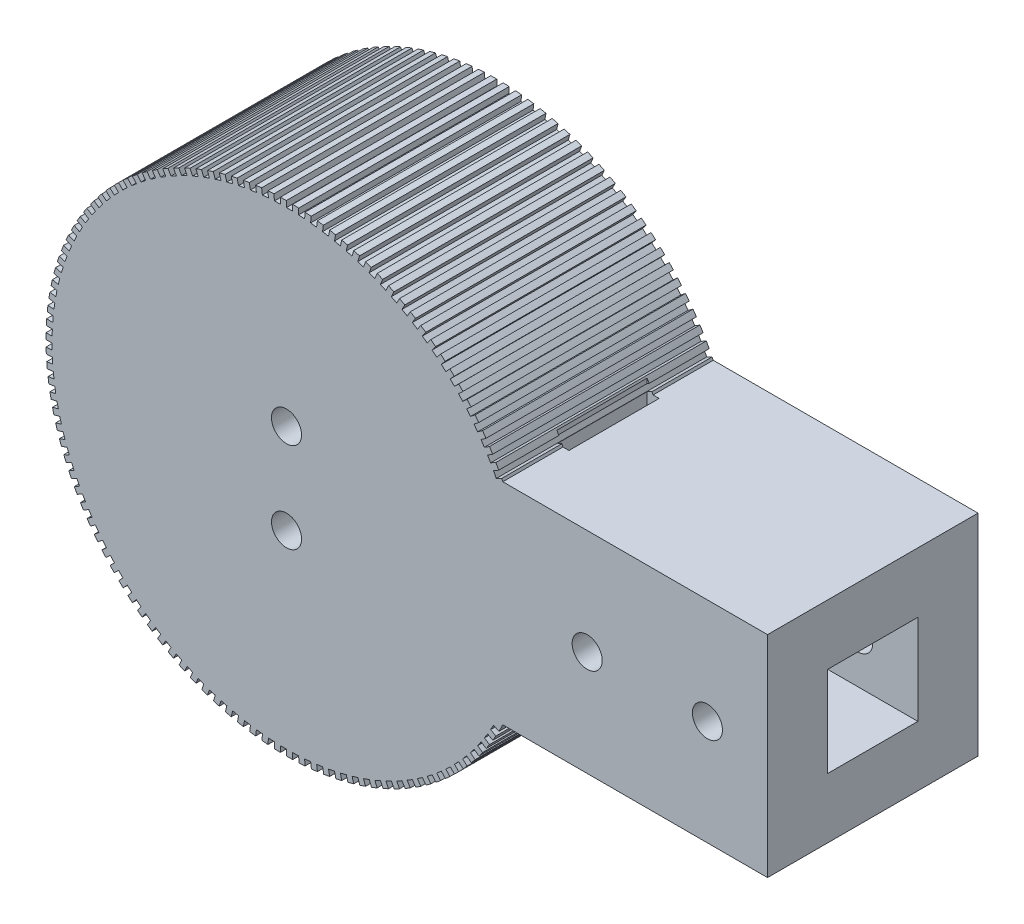
SolidWorks part; units mm, degrees
ref_plane "Front Plane" through (0, 0, 0) normal (0, 0, 1) x (1, 0, 0)
ref_plane "Top Plane" through (0, 0, 0) normal (0, 1, 0) x (1, 0, 0)
ref_plane "Right Plane" through (0, 0, 0) normal (1, 0, 0) x (0, 0, -1)
sketch "Sketch1" plane through (0, 0, 0) normal (0, 0, 1) x (1, 0, 0)
  circle A0 centre (0, 0) radius 40
  dimension "D1" = 80
extrude "Boss-Extrude1" add sketch "Sketch1" along normal blind 35
sketch "Sketch2" plane through (0, 0, 0) normal (1, 0, 0) x (0, 0, -1)
  line L0 (0, 0) -> (-35, 0) construction
  line L1 (-35, 40) -> (-35, -40) construction
  line L2 (0, -40) -> (0, 40) construction
  line L3 (-35, -17.5) -> (0, -17.5)
  line L4 (-35, -17.5) -> (-35, 17.5)
  line L5 (-35, 17.5) -> (0, 17.5)
  line L6 (0, -17.5) -> (0, 17.5)
  line L7 (-35, -17.5) -> (0, 17.5) construction
  line L8 (-35, 17.5) -> (0, -17.5) construction
  line L14 (-27.2632, -9.7632) -> (-6.2129, 11.2871) construction
  line L15 (-25, 12.8571) -> (-10, -12.8571) construction
  point P5 (-17.5, 0)
  point P12 (-17.5, 0)
  dimension "D1" = 35
extrude "Boss-Extrude2" add sketch "Sketch2" along normal blind 80
sketch "Sketch3" plane through (0, 0, 0) normal (0, 0, -1) x (-1, 0, 0)
  circle A0 centre (0, 0) radius 7.5 construction
  circle A1 centre (0, 7.5) radius 2.5
  circle A2 centre (0, -7.5) radius 2.5
  circle A3 centre (0, 0) radius 1.25
  dimension "D1" = 5
  dimension "D2" = 15
extrude "Cut-Extrude1" cut sketch "Sketch3" against normal through all both and the other way through all contours A2 | A1
sketch "Sketch4" plane through (0, 17.5, 0) normal (0, 1, 0) x (1, 0, 0)
  line L0 (35.9687, 0) -> (35.9687, -35) construction
  line L2 (34.9687, -25) -> (36.9687, -25)
  line L3 (34.9687, -25) -> (34.9687, -10)
  line L4 (34.9687, -10) -> (36.9687, -10)
  line L5 (36.9687, -25) -> (36.9687, -10)
  line L6 (34.9687, -25) -> (36.9687, -10) construction
  line L7 (34.9687, -10) -> (36.9687, -25) construction
  point P4 (35.9687, -17.5)
  dimension "D1" = 2
  dimension "D2" = 15
extrude "Cut-Extrude2" cut sketch "Sketch4" against normal through all both and the other way through all
sketch "Sketch6" plane through (80, 0, 0) normal (1, 0, 0) x (0, 0, -1)
  line L0 (-35, 17.5) -> (0, -17.5) construction
  line L2 (-10, -7.5) -> (-25, -7.5)
  line L3 (-10, -7.5) -> (-10, 7.5)
  line L4 (-10, 7.5) -> (-25, 7.5)
  line L5 (-25, -7.5) -> (-25, 7.5)
  line L6 (-10, -7.5) -> (-25, 7.5) construction
  line L7 (-10, 7.5) -> (-25, -7.5) construction
  point P4 (-17.5, 0)
  dimension "D1" = 15
  dimension "D2" = 15
extrude "Cut-Extrude4" cut sketch "Sketch6" against normal blind 47.5
sketch "Sketch7" plane through (0, 0, 35) normal (0, 0, 1) x (1, 0, 0)
  line L1 (80, -17.5) -> (80, 17.5) construction
  line L2 (40, 0) -> (60, 0) construction
  line L3 (60, 0) -> (80, 0) construction
  circle A0 centre (50, 0) radius 2.5
  circle A1 centre (70, 0) radius 2.5
  dimension "D2" = 5
  dimension "D3" = 5
  dimension "D1" = 40
extrude "Cut-Extrude5" cut sketch "Sketch7" against normal through all both and the other way through all
sketch "Sketch8" plane through (0, 0, 35) normal (0, 0, 1) x (1, 0, 0)
  line L0 (0, 0) -> (-40.0066, 0) construction
  line L1 (-39, 0) -> (-40.0066, 0)
  line L2 (-40.0066, 0) -> (-39.9941, 1)
  line L3 (-39.9941, 1) -> (-38.9872, 1)
  line L4 (-38.9483, 2.0077) -> (-39.9536, 2.0595)
  line L5 (-39.9536, 2.0595) -> (-39.8896, 3.0575)
  line L6 (-39.8896, 3.0575) -> (-38.884, 3.0057)
  line L7 (-38.7933, 4.01) -> (-39.7946, 4.1135)
  line L8 (-39.7946, 4.1135) -> (-39.6793, 5.1069)
  line L9 (-39.6793, 5.1069) -> (-38.6777, 5.0034)
  line L10 (-38.5354, 6.0017) -> (-39.5301, 6.1566)
  line L11 (-39.5301, 6.1566) -> (-39.3638, 7.1428)
  line L12 (-39.3638, 7.1428) -> (-38.3689, 6.9878)
  line L13 (-38.1754, 7.9775) -> (-39.1607, 8.1834)
  line L14 (-39.1607, 8.1834) -> (-38.9439, 9.1597)
  line L15 (-38.9439, 9.1597) -> (-37.9583, 8.9538)
  line L16 (-37.7141, 9.9322) -> (-38.6875, 10.1885)
  line L17 (-38.6875, 10.1885) -> (-38.4208, 11.1524)
  line L18 (-38.4208, 11.1524) -> (-37.447, 10.8959)
  line L19 (-37.1528, 11.8605) -> (-38.1117, 12.1666)
  line L20 (-38.1117, 12.1666) -> (-37.7957, 13.1154)
  line L21 (-37.7957, 13.1154) -> (-36.8364, 12.8092)
  line L22 (-36.493, 13.7573) -> (-37.4349, 14.1124)
  line L23 (-37.4349, 14.1124) -> (-37.0704, 15.0437)
  line L24 (-37.0704, 15.0437) -> (-36.1282, 14.6885)
  line L25 (-35.7364, 15.6177) -> (-36.6588, 16.0208)
  line L26 (-36.6588, 16.0208) -> (-36.2469, 16.9321)
  line L27 (-36.2469, 16.9321) -> (-35.3242, 16.5289)
  line L28 (-34.885, 17.4367) -> (-35.7854, 17.8867)
  line L29 (-35.7854, 17.8867) -> (-35.3271, 18.7756)
  line L30 (-35.3271, 18.7756) -> (-34.4264, 18.3254)
  line L31 (-33.9411, 19.2094) -> (-34.8172, 19.7052)
  line L32 (-34.8172, 19.7052) -> (-34.3138, 20.5693)
  line L33 (-34.3138, 20.5693) -> (-33.4374, 20.0733)
  line L34 (-32.9072, 20.9312) -> (-33.7566, 21.4714)
  line L35 (-33.7566, 21.4714) -> (-33.2094, 22.3085)
  line L36 (-33.2094, 22.3085) -> (-32.3597, 21.768)
  line L37 (-31.7861, 22.5974) -> (-32.6065, 23.1807)
  line L38 (-32.6065, 23.1807) -> (-32.0169, 23.9885)
  line L39 (-32.0169, 23.9885) -> (-31.1962, 23.405)
  line L40 (-30.5807, 24.2038) -> (-31.37, 24.8285)
  line L41 (-31.37, 24.8285) -> (-30.7396, 25.6049)
  line L42 (-30.7396, 25.6049) -> (-29.95, 24.9799)
  line L43 (-29.2941, 25.7459) -> (-30.0503, 26.4105)
  line L44 (-30.0503, 26.4105) -> (-29.3807, 27.1533)
  line L45 (-29.3807, 27.1533) -> (-28.6244, 26.4886)
  line L46 (-27.9299, 27.2198) -> (-28.6508, 27.9224)
  line L47 (-28.6508, 27.9224) -> (-27.9439, 28.6298)
  line L48 (-27.9439, 28.6298) -> (-27.2228, 27.927)
  line L49 (-26.4917, 28.6215) -> (-27.1754, 29.3603)
  line L50 (-27.1754, 29.3603) -> (-26.4331, 30.0304)
  line L51 (-26.4331, 30.0304) -> (-25.7491, 29.2914)
  line L52 (-24.9831, 29.9473) -> (-25.628, 30.7203)
  line L53 (-25.628, 30.7203) -> (-24.8521, 31.3513)
  line L54 (-24.8521, 31.3513) -> (-24.207, 30.5781)
  line L55 (-23.4084, 31.1937) -> (-24.0126, 31.9989)
  line L56 (-24.0126, 31.9989) -> (-23.2052, 32.5891)
  line L57 (-23.2052, 32.5891) -> (-22.6008, 31.7837)
  line L58 (-21.7715, 32.3574) -> (-22.3335, 33.1926)
  line L59 (-22.3335, 33.1926) -> (-21.4968, 33.7405)
  line L60 (-21.4968, 33.7405) -> (-20.9347, 32.905)
  line L61 (-20.0769, 33.4353) -> (-20.5951, 34.2983)
  line L62 (-20.5951, 34.2983) -> (-19.7314, 34.8024)
  line L63 (-19.7314, 34.8024) -> (-19.213, 33.9391)
  line L64 (-18.3291, 34.4245) -> (-18.8022, 35.313)
  line L65 (-18.8022, 35.313) -> (-17.9136, 35.772)
  line L66 (-17.9136, 35.772) -> (-17.4404, 34.8831)
  line L67 (-16.5327, 35.3224) -> (-16.9594, 36.2341)
  line L68 (-16.9594, 36.2341) -> (-16.0484, 36.6467)
  line L69 (-16.0484, 36.6467) -> (-15.6215, 35.7347)
  line L70 (-14.6924, 36.1266) -> (-15.0716, 37.0591)
  line L71 (-15.0716, 37.0591) -> (-14.1406, 37.4243)
  line L72 (-14.1406, 37.4243) -> (-13.7612, 36.4915)
  line L73 (-12.8132, 36.8351) -> (-13.1439, 37.7858)
  line L74 (-13.1439, 37.7858) -> (-12.1953, 38.1026)
  line L75 (-12.1953, 38.1026) -> (-11.8645, 37.1515)
  line L76 (-10.8999, 37.4458) -> (-11.1813, 38.4124)
  line L77 (-11.1813, 38.4124) -> (-10.2176, 38.6799)
  line L78 (-10.2176, 38.6799) -> (-9.9362, 37.713)
  line L79 (-8.9578, 37.9573) -> (-9.189, 38.937)
  line L80 (-9.189, 38.937) -> (-8.2129, 39.1546)
  line L81 (-8.2129, 39.1546) -> (-7.9816, 38.1745)
  line L82 (-6.9919, 38.3681) -> (-7.1724, 39.3584)
  line L83 (-7.1724, 39.3584) -> (-6.1864, 39.5254)
  line L84 (-6.1864, 39.5254) -> (-6.0059, 38.5348)
  line L85 (-5.0075, 38.6772) -> (-5.1368, 39.6755)
  line L86 (-5.1368, 39.6755) -> (-4.1435, 39.7915)
  line L87 (-4.1435, 39.7915) -> (-4.0142, 38.7929)
  line L88 (-3.0098, 38.8837) -> (-3.0875, 39.8873)
  line L89 (-3.0875, 39.8873) -> (-2.0895, 39.952)
  line L90 (-2.0895, 39.952) -> (-2.0118, 38.9481)
  line L91 (-1.0042, 38.9871) -> (-1.0301, 39.9934)
  line L92 (-1.0301, 39.9934) -> (-0.0301, 40.0066)
  line L93 (-0.0301, 40.0066) -> (-0.0042, 39)
  line L94 (1.0042, 38.9871) -> (1.0301, 39.9934)
  line L95 (1.0301, 39.9934) -> (2.0294, 39.9551)
  line L96 (2.0294, 39.9551) -> (2.0035, 38.9485)
  line L97 (3.0098, 38.8837) -> (3.0875, 39.8873)
  line L98 (3.0875, 39.8873) -> (4.0836, 39.7977)
  line L99 (4.0836, 39.7977) -> (4.0059, 38.7937)
  line L100 (5.0075, 38.6772) -> (5.1368, 39.6755)
  line L101 (5.1368, 39.6755) -> (6.1269, 39.5347)
  line L102 (6.1269, 39.5347) -> (5.9976, 38.5361)
  line L103 (6.9919, 38.3681) -> (7.1724, 39.3584)
  line L104 (7.1724, 39.3584) -> (8.154, 39.1669)
  line L105 (8.154, 39.1669) -> (7.9734, 38.1762)
  line L106 (8.9578, 37.9573) -> (9.189, 38.937)
  line L107 (9.189, 38.937) -> (10.1594, 38.6952)
  line L108 (10.1594, 38.6952) -> (9.9281, 37.7151)
  line L109 (10.8999, 37.4458) -> (11.1813, 38.4124)
  line L110 (11.1813, 38.4124) -> (12.1379, 38.1209)
  line L111 (12.1379, 38.1209) -> (11.8565, 37.154)
  line L112 (12.8132, 36.8351) -> (13.1439, 37.7858)
  line L113 (13.1439, 37.7858) -> (14.0843, 37.4455)
  line L114 (14.0843, 37.4455) -> (13.7534, 36.4944)
  line L115 (14.6924, 36.1266) -> (15.0716, 37.0591)
  line L116 (15.0716, 37.0591) -> (15.9932, 36.6708)
  line L117 (15.9932, 36.6708) -> (15.6139, 35.738)
  line L118 (16.5327, 35.3224) -> (16.9594, 36.2341)
  line L119 (16.9594, 36.2341) -> (17.8598, 35.7989)
  line L120 (17.8598, 35.7989) -> (17.4329, 34.8869)
  line L121 (18.3291, 34.4245) -> (18.8022, 35.313)
  line L122 (18.8022, 35.313) -> (19.679, 34.832)
  line L123 (19.679, 34.832) -> (19.2057, 33.9432)
  line L124 (20.0769, 33.4353) -> (20.5951, 34.2983)
  line L125 (20.5951, 34.2983) -> (21.446, 33.7728)
  line L126 (21.446, 33.7728) -> (20.9276, 32.9095)
  line L127 (21.7715, 32.3574) -> (22.3335, 33.1926)
  line L128 (22.3335, 33.1926) -> (23.1562, 32.624)
  line L129 (23.1562, 32.624) -> (22.594, 31.7885)
  line L130 (23.4084, 31.1937) -> (24.0126, 31.9989)
  line L131 (24.0126, 31.9989) -> (24.8049, 31.3887)
  line L132 (24.8049, 31.3887) -> (24.2005, 30.5833)
  line L133 (24.9831, 29.9473) -> (25.628, 30.7203)
  line L134 (25.628, 30.7203) -> (26.3879, 30.0701)
  line L135 (26.3879, 30.0701) -> (25.7428, 29.2969)
  line L136 (26.4917, 28.6215) -> (27.1754, 29.3603)
  line L137 (27.1754, 29.3603) -> (27.9008, 28.6718)
  line L138 (27.9008, 28.6718) -> (27.2168, 27.9328)
  line L139 (27.9299, 27.2198) -> (28.6508, 27.9224)
  line L140 (28.6508, 27.9224) -> (29.3398, 27.1975)
  line L141 (29.3398, 27.1975) -> (28.6187, 26.4947)
  line L142 (29.2941, 25.7459) -> (30.0503, 26.4105)
  line L143 (30.0503, 26.4105) -> (30.701, 25.6511)
  line L144 (30.701, 25.6511) -> (29.9447, 24.9863)
  line L145 (30.5807, 24.2038) -> (31.37, 24.8285)
  line L146 (31.37, 24.8285) -> (31.9808, 24.0366)
  line L147 (31.9808, 24.0366) -> (31.1912, 23.4117)
  line L148 (31.7861, 22.5974) -> (32.6065, 23.1807)
  line L149 (32.6065, 23.1807) -> (33.1758, 22.3584)
  line L150 (33.1758, 22.3584) -> (32.3551, 21.775)
  line L151 (32.9072, 20.9312) -> (33.7566, 21.4714)
  line L152 (33.7566, 21.4714) -> (34.2828, 20.6209)
  line L153 (34.2828, 20.6209) -> (33.4331, 20.0805)
  line L154 (33.9411, 19.2094) -> (34.8172, 19.7052)
  line L155 (34.8172, 19.7052) -> (35.2989, 18.8288)
  line L156 (35.2989, 18.8288) -> (34.4225, 18.3328)
  line L157 (34.885, 17.4367) -> (35.7854, 17.8867)
  line L212 (35.7854, -17.8867) -> (35.3271, -18.7756)
  line L213 (35.3271, -18.7756) -> (34.4264, -18.3254)
  line L214 (33.9411, -19.2094) -> (34.8172, -19.7052)
  line L215 (34.8172, -19.7052) -> (34.3138, -20.5693)
  line L216 (34.3138, -20.5693) -> (33.4374, -20.0733)
  line L217 (32.9072, -20.9312) -> (33.7566, -21.4714)
  line L218 (33.7566, -21.4714) -> (33.2094, -22.3085)
  line L219 (33.2094, -22.3085) -> (32.3597, -21.768)
  line L220 (31.7861, -22.5974) -> (32.6065, -23.1807)
  line L221 (32.6065, -23.1807) -> (32.0169, -23.9885)
  line L222 (32.0169, -23.9885) -> (31.1962, -23.405)
  line L223 (30.5807, -24.2038) -> (31.37, -24.8285)
  line L224 (31.37, -24.8285) -> (30.7396, -25.6049)
  line L225 (30.7396, -25.6049) -> (29.95, -24.9799)
  line L226 (29.2941, -25.7459) -> (30.0503, -26.4105)
  line L227 (30.0503, -26.4105) -> (29.3807, -27.1533)
  line L228 (29.3807, -27.1533) -> (28.6244, -26.4886)
  line L229 (27.9299, -27.2198) -> (28.6508, -27.9224)
  line L230 (28.6508, -27.9224) -> (27.9439, -28.6298)
  line L231 (27.9439, -28.6298) -> (27.2228, -27.927)
  line L232 (26.4917, -28.6215) -> (27.1754, -29.3603)
  line L233 (27.1754, -29.3603) -> (26.4331, -30.0304)
  line L234 (26.4331, -30.0304) -> (25.7491, -29.2914)
  line L235 (24.9831, -29.9473) -> (25.628, -30.7203)
  line L236 (25.628, -30.7203) -> (24.8521, -31.3513)
  line L237 (24.8521, -31.3513) -> (24.207, -30.5781)
  line L238 (23.4084, -31.1937) -> (24.0126, -31.9989)
  line L239 (24.0126, -31.9989) -> (23.2052, -32.5891)
  line L240 (23.2052, -32.5891) -> (22.6008, -31.7837)
  line L241 (21.7715, -32.3574) -> (22.3335, -33.1926)
  line L242 (22.3335, -33.1926) -> (21.4968, -33.7405)
  line L243 (21.4968, -33.7405) -> (20.9347, -32.905)
  line L244 (20.0769, -33.4353) -> (20.5951, -34.2983)
  line L245 (20.5951, -34.2983) -> (19.7314, -34.8024)
  line L246 (19.7314, -34.8024) -> (19.213, -33.9391)
  line L247 (18.3291, -34.4245) -> (18.8022, -35.313)
  line L248 (18.8022, -35.313) -> (17.9136, -35.772)
  line L249 (17.9136, -35.772) -> (17.4404, -34.8831)
  line L250 (16.5327, -35.3224) -> (16.9594, -36.2341)
  line L251 (16.9594, -36.2341) -> (16.0484, -36.6467)
  line L252 (16.0484, -36.6467) -> (15.6215, -35.7347)
  line L253 (14.6924, -36.1266) -> (15.0716, -37.0591)
  line L254 (15.0716, -37.0591) -> (14.1406, -37.4243)
  line L255 (14.1406, -37.4243) -> (13.7612, -36.4915)
  line L256 (12.8132, -36.8351) -> (13.1439, -37.7858)
  line L257 (13.1439, -37.7858) -> (12.1953, -38.1026)
  line L258 (12.1953, -38.1026) -> (11.8645, -37.1515)
  line L259 (10.8999, -37.4458) -> (11.1813, -38.4124)
  line L260 (11.1813, -38.4124) -> (10.2176, -38.6799)
  line L261 (10.2176, -38.6799) -> (9.9362, -37.713)
  line L262 (8.9578, -37.9573) -> (9.189, -38.937)
  line L263 (9.189, -38.937) -> (8.2129, -39.1546)
  line L264 (8.2129, -39.1546) -> (7.9816, -38.1745)
  line L265 (6.9919, -38.3681) -> (7.1724, -39.3584)
  line L266 (7.1724, -39.3584) -> (6.1864, -39.5254)
  line L267 (6.1864, -39.5254) -> (6.0059, -38.5348)
  line L268 (5.0075, -38.6772) -> (5.1368, -39.6755)
  line L269 (5.1368, -39.6755) -> (4.1435, -39.7915)
  line L270 (4.1435, -39.7915) -> (4.0142, -38.7929)
  line L271 (3.0098, -38.8837) -> (3.0875, -39.8873)
  line L272 (3.0875, -39.8873) -> (2.0895, -39.952)
  line L273 (2.0895, -39.952) -> (2.0118, -38.9481)
  line L274 (1.0042, -38.9871) -> (1.0301, -39.9934)
  line L275 (1.0301, -39.9934) -> (0.0301, -40.0066)
  line L276 (0.0301, -40.0066) -> (0.0042, -39)
  line L277 (-1.0042, -38.9871) -> (-1.0301, -39.9934)
  line L278 (-1.0301, -39.9934) -> (-2.0294, -39.9551)
  line L279 (-2.0294, -39.9551) -> (-2.0035, -38.9485)
  line L280 (-3.0098, -38.8837) -> (-3.0875, -39.8873)
  line L281 (-3.0875, -39.8873) -> (-4.0836, -39.7977)
  line L282 (-4.0836, -39.7977) -> (-4.0059, -38.7937)
  line L283 (-5.0075, -38.6772) -> (-5.1368, -39.6755)
  line L284 (-5.1368, -39.6755) -> (-6.1269, -39.5347)
  line L285 (-6.1269, -39.5347) -> (-5.9976, -38.5361)
  line L286 (-6.9919, -38.3681) -> (-7.1724, -39.3584)
  line L287 (-7.1724, -39.3584) -> (-8.154, -39.1669)
  line L288 (-8.154, -39.1669) -> (-7.9734, -38.1762)
  line L289 (-8.9578, -37.9573) -> (-9.189, -38.937)
  line L290 (-9.189, -38.937) -> (-10.1594, -38.6952)
  line L291 (-10.1594, -38.6952) -> (-9.9281, -37.7151)
  line L292 (-10.8999, -37.4458) -> (-11.1813, -38.4124)
  line L293 (-11.1813, -38.4124) -> (-12.1379, -38.1209)
  line L294 (-12.1379, -38.1209) -> (-11.8565, -37.154)
  line L295 (-12.8132, -36.8351) -> (-13.1439, -37.7858)
  line L296 (-13.1439, -37.7858) -> (-14.0843, -37.4455)
  line L297 (-14.0843, -37.4455) -> (-13.7534, -36.4944)
  line L298 (-14.6924, -36.1266) -> (-15.0716, -37.0591)
  line L299 (-15.0716, -37.0591) -> (-15.9932, -36.6708)
  line L300 (-15.9932, -36.6708) -> (-15.6139, -35.738)
  line L301 (-16.5327, -35.3224) -> (-16.9594, -36.2341)
  line L302 (-16.9594, -36.2341) -> (-17.8598, -35.7989)
  line L303 (-17.8598, -35.7989) -> (-17.4329, -34.8869)
  line L304 (-18.3291, -34.4245) -> (-18.8022, -35.313)
  line L305 (-18.8022, -35.313) -> (-19.679, -34.832)
  line L306 (-19.679, -34.832) -> (-19.2057, -33.9432)
  line L307 (-20.0769, -33.4353) -> (-20.5951, -34.2983)
  line L308 (-20.5951, -34.2983) -> (-21.446, -33.7728)
  line L309 (-21.446, -33.7728) -> (-20.9276, -32.9095)
  line L310 (-21.7715, -32.3574) -> (-22.3335, -33.1926)
  line L311 (-22.3335, -33.1926) -> (-23.1562, -32.624)
  line L312 (-23.1562, -32.624) -> (-22.594, -31.7885)
  line L313 (-23.4084, -31.1937) -> (-24.0126, -31.9989)
  line L314 (-24.0126, -31.9989) -> (-24.8049, -31.3887)
  line L315 (-24.8049, -31.3887) -> (-24.2005, -30.5833)
  line L316 (-24.9831, -29.9473) -> (-25.628, -30.7203)
  line L317 (-25.628, -30.7203) -> (-26.3879, -30.0701)
  line L318 (-26.3879, -30.0701) -> (-25.7428, -29.2969)
  line L319 (-26.4917, -28.6215) -> (-27.1754, -29.3603)
  line L320 (-27.1754, -29.3603) -> (-27.9008, -28.6718)
  line L321 (-27.9008, -28.6718) -> (-27.2168, -27.9328)
  line L322 (-27.9299, -27.2198) -> (-28.6508, -27.9224)
  line L323 (-28.6508, -27.9224) -> (-29.3398, -27.1975)
  line L324 (-29.3398, -27.1975) -> (-28.6187, -26.4947)
  line L325 (-29.2941, -25.7459) -> (-30.0503, -26.4105)
  line L326 (-30.0503, -26.4105) -> (-30.701, -25.6511)
  line L327 (-30.701, -25.6511) -> (-29.9447, -24.9863)
  line L328 (-30.5807, -24.2038) -> (-31.37, -24.8285)
  line L329 (-31.37, -24.8285) -> (-31.9808, -24.0366)
  line L330 (-31.9808, -24.0366) -> (-31.1912, -23.4117)
  line L331 (-31.7861, -22.5974) -> (-32.6065, -23.1807)
  line L332 (-32.6065, -23.1807) -> (-33.1758, -22.3584)
  line L333 (-33.1758, -22.3584) -> (-32.3551, -21.775)
  line L334 (-32.9072, -20.9312) -> (-33.7566, -21.4714)
  line L335 (-33.7566, -21.4714) -> (-34.2828, -20.6209)
  line L336 (-34.2828, -20.6209) -> (-33.4331, -20.0805)
  line L337 (-33.9411, -19.2094) -> (-34.8172, -19.7052)
  line L338 (-34.8172, -19.7052) -> (-35.2989, -18.8288)
  line L339 (-35.2989, -18.8288) -> (-34.4225, -18.3328)
  line L340 (-34.885, -17.4367) -> (-35.7854, -17.8867)
  line L341 (-35.7854, -17.8867) -> (-36.2213, -16.9866)
  line L342 (-36.2213, -16.9866) -> (-35.3206, -16.5364)
  line L343 (-35.7364, -15.6177) -> (-36.6588, -16.0208)
  line L344 (-36.6588, -16.0208) -> (-37.0478, -15.0995)
  line L345 (-37.0478, -15.0995) -> (-36.1251, -14.6963)
  line L346 (-36.493, -13.7573) -> (-37.4349, -14.1124)
  line L347 (-37.4349, -14.1124) -> (-37.7759, -13.1723)
  line L348 (-37.7759, -13.1723) -> (-36.8337, -12.8171)
  line L349 (-37.1528, -11.8605) -> (-38.1117, -12.1666)
  line L350 (-38.1117, -12.1666) -> (-38.4039, -11.2102)
  line L351 (-38.4039, -11.2102) -> (-37.4447, -10.9039)
  line L352 (-37.7141, -9.9322) -> (-38.6875, -10.1885)
  line L353 (-38.6875, -10.1885) -> (-38.9301, -9.2183)
  line L354 (-38.9301, -9.2183) -> (-37.9564, -8.9619)
  line L355 (-38.1754, -7.9775) -> (-39.1607, -8.1834)
  line L356 (-39.1607, -8.1834) -> (-39.353, -7.202)
  line L357 (-39.353, -7.202) -> (-38.3674, -6.9961)
  line L358 (-38.5354, -6.0017) -> (-39.5301, -6.1566)
  line L359 (-39.5301, -6.1566) -> (-39.6716, -5.1666)
  line L360 (-39.6716, -5.1666) -> (-38.6766, -5.0117)
  line L361 (-38.7933, -4.01) -> (-39.7946, -4.1135)
  line L362 (-39.7946, -4.1135) -> (-39.885, -3.1175)
  line L363 (-39.885, -3.1175) -> (-38.8834, -3.014)
  line L364 (-38.9483, -2.0077) -> (-39.9536, -2.0595)
  line L365 (-39.9536, -2.0595) -> (-39.9926, -1.0602)
  line L366 (-39.9926, -1.0602) -> (-38.987, -1.0083)
  line L367 (-38.987, -1.0083) -> (-39, 0)
  line L368 (-38.9872, 1) -> (-38.9483, 2.0077)
  line L369 (-38.884, 3.0057) -> (-38.7933, 4.01)
  line L370 (-38.6777, 5.0034) -> (-38.5354, 6.0017)
  line L371 (-38.3689, 6.9878) -> (-38.1754, 7.9775)
  line L372 (-37.9583, 8.9538) -> (-37.7141, 9.9322)
  line L373 (-37.447, 10.8959) -> (-37.1528, 11.8605)
  line L374 (-36.8364, 12.8092) -> (-36.493, 13.7573)
  line L375 (-36.1282, 14.6885) -> (-35.7364, 15.6177)
  line L376 (-35.3242, 16.5289) -> (-34.885, 17.4367)
  line L377 (-34.4264, 18.3254) -> (-33.9411, 19.2094)
  line L378 (-33.4374, 20.0733) -> (-32.9072, 20.9312)
  line L379 (-32.3597, 21.768) -> (-31.7861, 22.5974)
  line L380 (-31.1962, 23.405) -> (-30.5807, 24.2038)
  line L381 (-29.95, 24.9799) -> (-29.2941, 25.7459)
  line L382 (-28.6244, 26.4886) -> (-27.9299, 27.2198)
  line L383 (-27.2228, 27.927) -> (-26.4917, 28.6215)
  line L384 (-25.7491, 29.2914) -> (-24.9831, 29.9473)
  line L385 (-24.207, 30.5781) -> (-23.4084, 31.1937)
  line L386 (-22.6008, 31.7837) -> (-21.7715, 32.3574)
  line L387 (-20.9347, 32.905) -> (-20.0769, 33.4353)
  line L388 (-19.213, 33.9391) -> (-18.3291, 34.4245)
  line L389 (-17.4404, 34.8831) -> (-16.5327, 35.3224)
  line L390 (-15.6215, 35.7347) -> (-14.6924, 36.1266)
  line L391 (-13.7612, 36.4915) -> (-12.8132, 36.8351)
  line L392 (-11.8645, 37.1515) -> (-10.8999, 37.4458)
  line L393 (-9.9362, 37.713) -> (-8.9578, 37.9573)
  line L394 (-7.9816, 38.1745) -> (-6.9919, 38.3681)
  line L395 (-6.0059, 38.5348) -> (-5.0075, 38.6772)
  line L396 (-4.0142, 38.7929) -> (-3.0098, 38.8837)
  line L397 (-2.0118, 38.9481) -> (-1.0042, 38.9871)
  line L398 (-0.0042, 39) -> (1.0042, 38.9871)
  line L399 (2.0035, 38.9485) -> (3.0098, 38.8837)
  line L400 (4.0059, 38.7937) -> (5.0075, 38.6772)
  line L401 (5.9976, 38.5361) -> (6.9919, 38.3681)
  line L402 (7.9734, 38.1762) -> (8.9578, 37.9573)
  line L403 (9.9281, 37.7151) -> (10.8999, 37.4458)
  line L404 (11.8565, 37.154) -> (12.8132, 36.8351)
  line L405 (13.7534, 36.4944) -> (14.6924, 36.1266)
  line L406 (15.6139, 35.738) -> (16.5327, 35.3224)
  line L407 (17.4329, 34.8869) -> (18.3291, 34.4245)
  line L408 (19.2057, 33.9432) -> (20.0769, 33.4353)
  line L409 (20.9276, 32.9095) -> (21.7715, 32.3574)
  line L410 (22.594, 31.7885) -> (23.4084, 31.1937)
  line L411 (24.2005, 30.5833) -> (24.9831, 29.9473)
  line L412 (25.7428, 29.2969) -> (26.4917, 28.6215)
  line L413 (27.2168, 27.9328) -> (27.9299, 27.2198)
  line L414 (28.6187, 26.4947) -> (29.2941, 25.7459)
  line L415 (29.9447, 24.9863) -> (30.5807, 24.2038)
  line L416 (31.1912, 23.4117) -> (31.7861, 22.5974)
  line L417 (32.3551, 21.775) -> (32.9072, 20.9312)
  line L418 (33.4331, 20.0805) -> (33.9411, 19.2094)
  line L419 (34.4225, 18.3328) -> (34.885, 17.4367)
  line L438 (34.4264, -18.3254) -> (33.9411, -19.2094)
  line L439 (33.4374, -20.0733) -> (32.9072, -20.9312)
  line L440 (32.3597, -21.768) -> (31.7861, -22.5974)
  line L441 (31.1962, -23.405) -> (30.5807, -24.2038)
  line L442 (29.95, -24.9799) -> (29.2941, -25.7459)
  line L443 (28.6244, -26.4886) -> (27.9299, -27.2198)
  line L444 (27.2228, -27.927) -> (26.4917, -28.6215)
  line L445 (25.7491, -29.2914) -> (24.9831, -29.9473)
  line L446 (24.207, -30.5781) -> (23.4084, -31.1937)
  line L447 (22.6008, -31.7837) -> (21.7715, -32.3574)
  line L448 (20.9347, -32.905) -> (20.0769, -33.4353)
  line L449 (19.213, -33.9391) -> (18.3291, -34.4245)
  line L450 (17.4404, -34.8831) -> (16.5327, -35.3224)
  line L451 (15.6215, -35.7347) -> (14.6924, -36.1266)
  line L452 (13.7612, -36.4915) -> (12.8132, -36.8351)
  line L453 (11.8645, -37.1515) -> (10.8999, -37.4458)
  line L454 (9.9362, -37.713) -> (8.9578, -37.9573)
  line L455 (7.9816, -38.1745) -> (6.9919, -38.3681)
  line L456 (6.0059, -38.5348) -> (5.0075, -38.6772)
  line L457 (4.0142, -38.7929) -> (3.0098, -38.8837)
  line L458 (2.0118, -38.9481) -> (1.0042, -38.9871)
  line L459 (0.0042, -39) -> (-1.0042, -38.9871)
  line L460 (-2.0035, -38.9485) -> (-3.0098, -38.8837)
  line L461 (-4.0059, -38.7937) -> (-5.0075, -38.6772)
  line L462 (-5.9976, -38.5361) -> (-6.9919, -38.3681)
  line L463 (-7.9734, -38.1762) -> (-8.9578, -37.9573)
  line L464 (-9.9281, -37.7151) -> (-10.8999, -37.4458)
  line L465 (-11.8565, -37.154) -> (-12.8132, -36.8351)
  line L466 (-13.7534, -36.4944) -> (-14.6924, -36.1266)
  line L467 (-15.6139, -35.738) -> (-16.5327, -35.3224)
  line L468 (-17.4329, -34.8869) -> (-18.3291, -34.4245)
  line L469 (-19.2057, -33.9432) -> (-20.0769, -33.4353)
  line L470 (-20.9276, -32.9095) -> (-21.7715, -32.3574)
  line L471 (-22.594, -31.7885) -> (-23.4084, -31.1937)
  line L472 (-24.2005, -30.5833) -> (-24.9831, -29.9473)
  line L473 (-25.7428, -29.2969) -> (-26.4917, -28.6215)
  line L474 (-27.2168, -27.9328) -> (-27.9299, -27.2198)
  line L475 (-28.6187, -26.4947) -> (-29.2941, -25.7459)
  line L476 (-29.9447, -24.9863) -> (-30.5807, -24.2038)
  line L477 (-31.1912, -23.4117) -> (-31.7861, -22.5974)
  line L478 (-32.3551, -21.775) -> (-32.9072, -20.9312)
  line L479 (-33.4331, -20.0805) -> (-33.9411, -19.2094)
  line L480 (-34.4225, -18.3328) -> (-34.885, -17.4367)
  line L481 (-35.3206, -16.5364) -> (-35.7364, -15.6177)
  line L482 (-36.1251, -14.6963) -> (-36.493, -13.7573)
  line L483 (-36.8337, -12.8171) -> (-37.1528, -11.8605)
  line L484 (-37.4447, -10.9039) -> (-37.7141, -9.9322)
  line L485 (-37.9564, -8.9619) -> (-38.1754, -7.9775)
  line L486 (-38.3674, -6.9961) -> (-38.5354, -6.0017)
  line L487 (-38.6766, -5.0117) -> (-38.7933, -4.01)
  line L488 (-38.8834, -3.014) -> (-38.9483, -2.0077)
  line L489 (35.7854, -17.8867) -> (45.7097, -22.8472)
  line L490 (35.7854, 17.8867) -> (45.7097, 22.8472)
  line L493 (37.4349, 14.1124) -> (37.7759, 13.1723) [skipped]
  line L494 (36.2213, 16.9866) -> (35.3206, 16.5364) [skipped]
  line L495 (35.7364, 15.6177) -> (36.6588, 16.0208) [skipped]
  line L496 (36.6588, 16.0208) -> (37.0478, 15.0995) [skipped]
  line L497 (37.0478, 15.0995) -> (36.1251, 14.6963) [skipped]
  line L498 (36.493, 13.7573) -> (37.4349, 14.1124) [skipped]
  line L499 (37.7759, 13.1723) -> (36.8337, 12.8171) [skipped]
  line L500 (37.1528, 11.8605) -> (38.1117, 12.1666) [skipped]
  line L501 (38.1117, 12.1666) -> (38.4039, 11.2102) [skipped]
  line L502 (38.4039, 11.2102) -> (37.4447, 10.9039) [skipped]
  line L503 (37.7141, 9.9322) -> (38.6875, 10.1885) [skipped]
  line L504 (38.6875, 10.1885) -> (38.9301, 9.2183) [skipped]
  line L505 (38.9301, 9.2183) -> (37.9564, 8.9619) [skipped]
  line L506 (38.1754, 7.9775) -> (39.1607, 8.1834) [skipped]
  line L507 (39.1607, 8.1834) -> (39.353, 7.202) [skipped]
  line L508 (39.353, 7.202) -> (38.3674, 6.9961) [skipped]
  line L509 (38.5354, 6.0017) -> (39.5301, 6.1566) [skipped]
  line L510 (39.5301, 6.1566) -> (39.6716, 5.1666) [skipped]
  line L511 (39.6716, 5.1666) -> (38.6766, 5.0117) [skipped]
  line L512 (38.7933, 4.01) -> (39.7946, 4.1135) [skipped]
  line L513 (39.7946, 4.1135) -> (39.885, 3.1175) [skipped]
  line L514 (39.885, 3.1175) -> (38.8834, 3.014) [skipped]
  line L515 (38.9483, 2.0077) -> (39.9536, 2.0595) [skipped]
  line L516 (39.9536, 2.0595) -> (39.9926, 1.0602) [skipped]
  line L517 (39.9926, 1.0602) -> (38.987, 1.0083) [skipped]
  line L518 (39, 0) -> (40.0066, 0) [skipped]
  line L519 (40.0066, 0) -> (39.9941, -1) [skipped]
  line L520 (39.9941, -1) -> (38.9872, -1) [skipped]
  line L521 (38.9483, -2.0077) -> (39.9536, -2.0595) [skipped]
  line L522 (39.9536, -2.0595) -> (39.8896, -3.0575) [skipped]
  line L523 (39.8896, -3.0575) -> (38.884, -3.0057) [skipped]
  line L524 (38.7933, -4.01) -> (39.7946, -4.1135) [skipped]
  line L525 (39.7946, -4.1135) -> (39.6793, -5.1069) [skipped]
  line L526 (39.6793, -5.1069) -> (38.6777, -5.0034) [skipped]
  line L527 (38.5354, -6.0017) -> (39.5301, -6.1566) [skipped]
  line L528 (39.5301, -6.1566) -> (39.3638, -7.1428) [skipped]
  line L529 (39.3638, -7.1428) -> (38.3689, -6.9878) [skipped]
  line L530 (38.1754, -7.9775) -> (39.1607, -8.1834) [skipped]
  line L531 (39.1607, -8.1834) -> (38.9439, -9.1597) [skipped]
  line L532 (38.9439, -9.1597) -> (37.9583, -8.9538) [skipped]
  line L533 (37.7141, -9.9322) -> (38.6875, -10.1885) [skipped]
  line L534 (38.6875, -10.1885) -> (38.4208, -11.1524) [skipped]
  line L535 (38.4208, -11.1524) -> (37.447, -10.8959) [skipped]
  line L536 (37.1528, -11.8605) -> (38.1117, -12.1666) [skipped]
  line L537 (38.1117, -12.1666) -> (37.7957, -13.1154) [skipped]
  line L538 (37.7957, -13.1154) -> (36.8364, -12.8092) [skipped]
  line L539 (36.493, -13.7573) -> (37.4349, -14.1124) [skipped]
  line L540 (37.4349, -14.1124) -> (37.0704, -15.0437) [skipped]
  line L541 (37.0704, -15.0437) -> (36.1282, -14.6885) [skipped]
  line L542 (35.7364, -15.6177) -> (36.6588, -16.0208) [skipped]
  line L543 (36.6588, -16.0208) -> (36.2469, -16.9321) [skipped]
  line L544 (36.2469, -16.9321) -> (35.3242, -16.5289) [skipped]
  line L545 (35.3206, 16.5364) -> (35.7364, 15.6177) [skipped]
  line L546 (36.1251, 14.6963) -> (36.493, 13.7573) [skipped]
  line L547 (36.8337, 12.8171) -> (37.1528, 11.8605) [skipped]
  line L548 (37.4447, 10.9039) -> (37.7141, 9.9322) [skipped]
  line L549 (37.9564, 8.9619) -> (38.1754, 7.9775) [skipped]
  line L550 (38.3674, 6.9961) -> (38.5354, 6.0017) [skipped]
  line L551 (38.6766, 5.0117) -> (38.7933, 4.01) [skipped]
  line L552 (38.8834, 3.014) -> (38.9483, 2.0077) [skipped]
  line L553 (38.987, 1.0083) -> (39, 0) [skipped]
  line L554 (38.9872, -1) -> (38.9483, -2.0077) [skipped]
  line L555 (38.884, -3.0057) -> (38.7933, -4.01) [skipped]
  line L556 (38.6777, -5.0034) -> (38.5354, -6.0017) [skipped]
  line L557 (38.3689, -6.9878) -> (38.1754, -7.9775) [skipped]
  line L558 (37.9583, -8.9538) -> (37.7141, -9.9322) [skipped]
  line L559 (37.447, -10.8959) -> (37.1528, -11.8605) [skipped]
  line L560 (36.8364, -12.8092) -> (36.493, -13.7573) [skipped]
  line L561 (36.1282, -14.6885) -> (35.7364, -15.6177) [skipped]
  line L562 (35.7854, 17.8867) -> (36.2213, 16.9866) [skipped]
  line L563 (35.3242, -16.5289) -> (34.885, -17.4367) [skipped]
  line L564 (34.885, -17.4367) -> (35.7854, -17.8867) [skipped]
  arc A2 (45.7097, 22.8472) -> (45.7097, -22.8472) centre (0, 0) ccw
  point P1 (0, 0)
  point P494 (0, 0)
  point P737 (0, 0)
  dimension "D2" = 1
  dimension "D3" = 122
  dimension "D4" = 122
extrude "Cut-Extrude9" cut sketch "Sketch8" against normal through all contours L212 L213 L438 L214 L215 L216 L439 L217 L218 L219 L440 L220 L221 L222 L441 L223 L224 L225 L442 L226 L227 L228 L443 L229 L230 L231 L444 L232 L233 L234 L445 L235 L236 L237 L446 L238 L239 L240 L447 L241 L242 L243 L448 L244 L245 L246 L449 L247 L248 L249 L450 L250 L251 L252 L451 L253 L254 L255 L452 L256 L257 L258 L453 L259 L260 L261 L454 L262 L263 L264 L455 L265 L266 L267 L456 L268 L269 L270 L457 L271 L272 L273 L458 L274 L275 L276 L459 L277 L278 L279 L460 L280 L281 L282 L461 L283 L284 L285 L462 L286 L287 L288 L463 L289 L290 L291 L464 L292 L293 L294 L465 L295 L296 L297 L466 L298 L299 L300 L467 L301 L302 L303 L468 L304 L305 L306 L469 L307 L308 L309 L470 L310 L311 L312 L471 L313 L314 L315 L472 L316 L317 L318 L473 L319 L320 L321 L474 L322 L323 L324 L475 L325 L326 L327 L476 L328 L329 L330 L477 L331 L332 L333 L478 L334 L335 L336 L479 L337 L338 L339 L480 L340 L341 L342 L481 L343 L344 L345 L482 L346 L347 L348 L483 L349 L350 L351 L484 L352 L353 L354 L485 L355 L356 L357 L486 L358 L359 L360 L487 L361 L362 L363 L488 L364 L365 L366 L367 L1 L2 L3 L368 L4 L5 L6 L369 L7 L8 L9 L370 L10 L11 L12 L371 L13 L14 L15 L372 L16 L17 L18 L373 L19 L20 L21 L374 L22 L23 L24 L375 L25 L26 L27 L376 L28 L29 L30 L377 L31 L32 L33 L378 L34 L35 L36 L379 L37 L38 L39 L380 L40 L41 L42 L381 L43 L44 L45 L382 L46 L47 L48 L383 L49 L50 L51 L384 L52 L53 L54 L385 L55 L56 L57 L386 L58 L59 L60 L387 L61 L62 L63 L388 L64 L65 L66 L389 L67 L68 L69 L390 L70 L71 L72 L391 L73 L74 L75 L392 L76 L77 L78 L393 L79 L80 L81 L394 L82 L83 L84 L395 L85 L86 L87 L396 L88 L89 L90 L397 L91 L92 L93 L398 L94 L95 L96 L399 L97 L98 L99 L400 L100 L101 L102 L401 L103 L104 L105 L402 L106 L107 L108 L403 L109 L110 L111 L404 L112 L113 L114 L405 L115 L116 L117 L406 L118 L119 L120 L407 L121 L122 L123 L408 L124 L125 L126 L409 L127 L128 L129 L410 L130 L131 L132 L411 L133 L134 L135 L412 L136 L137 L138 L413 L139 L140 L141 L414 L142 L143 L144 L415 L145 L146 L147 L416 L148 L149 L150 L417 L151 L152 L153 L418 L154 L155 L156 L419 L157 L490 A2 L489
